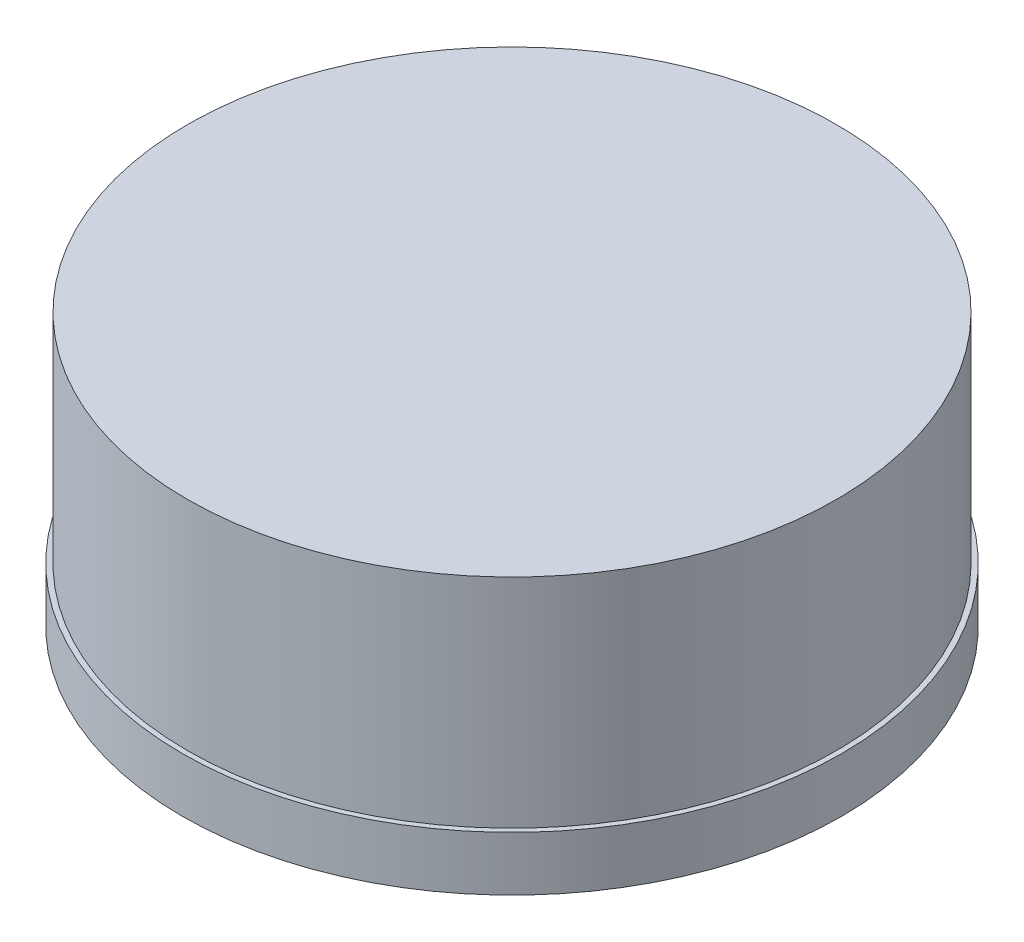
SolidWorks part; units mm, degrees
ref_plane "Front Plane" through (0, 0, 0) normal (0, 0, 1) x (1, 0, 0)
ref_plane "Top Plane" through (0, 0, 0) normal (0, 1, 0) x (1, 0, 0)
ref_plane "Right Plane" through (0, 0, 0) normal (1, 0, 0) x (0, 0, -1)
sketch "Sketch1" plane through (0, 0, 0) normal (0, 1, 0) x (1, 0, 0)
  circle A0 centre (0, 0) radius 4.85
extrude "Boss-Extrude1" add sketch "Sketch1" along normal blind 0.8
sketch "Sketch2" plane through (0, 0.8, 0) normal (0, 1, 0) x (1, 0, 0)
  circle A0 centre (0, 0) radius 4.775
extrude "Boss-Extrude2" add sketch "Sketch2" along normal blind 3.2
sketch "Sketch3" plane through (0, 0, 0) normal (0, -1, 0) x (-1, 0, 0)
  circle A0 centre (0, 0) radius 4.05
extrude "Cut-Extrude1" cut sketch "Sketch3" against normal blind 3.2
